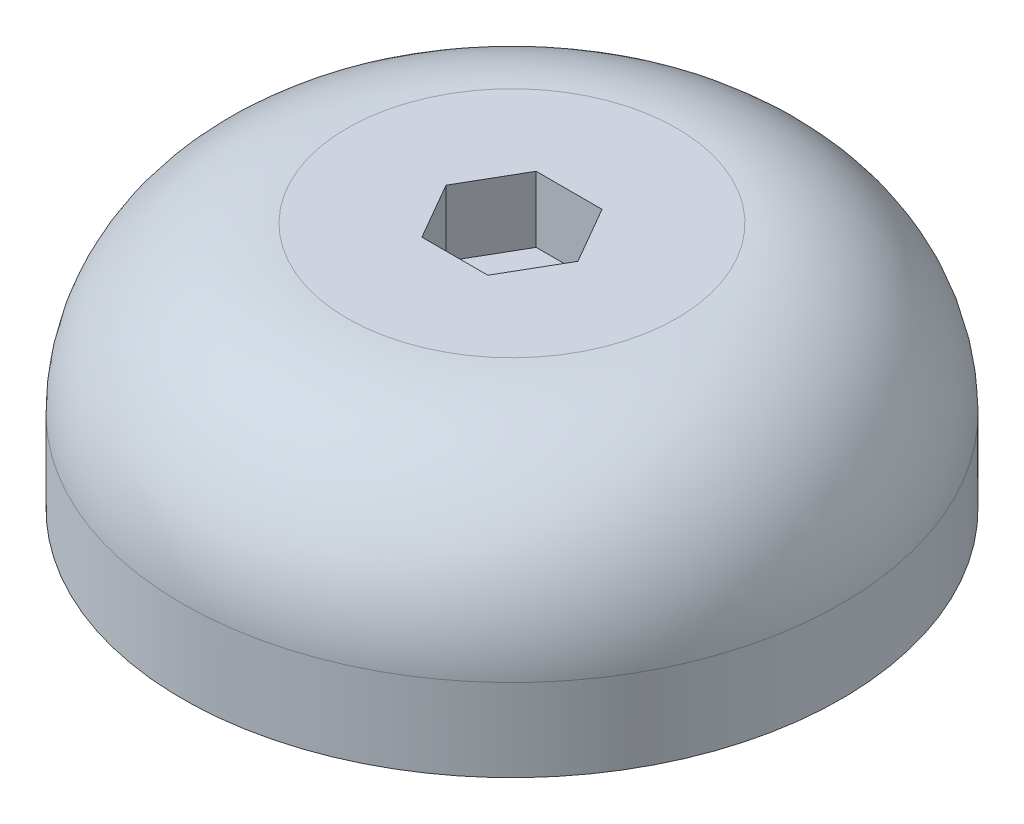
SolidWorks part; units mm, degrees
ref_plane "Front Plane" through (0, 0, 0) normal (0, 0, 1) x (1, 0, 0)
ref_plane "Top Plane" through (0, 0, 0) normal (0, 1, 0) x (1, 0, 0)
ref_plane "Right Plane" through (0, 0, 0) normal (1, 0, 0) x (0, 0, -1)
sketch "Sketch1" plane through (0, 0, 0) normal (0, 1, 0) x (1, 0, 0)
  circle A0 centre (0, 0) radius 9.75
  circle A1 centre (0, 0) radius 2
  dimension "D1" = 19.5
  dimension "D2" = 4
extrude "Boss-Extrude1" add sketch "Sketch1" along normal blind 3
sketch "Sketch2" plane through (0, 0, 0) normal (0, -1, 0) x (1, 0, 0)
  line L1 (-1.6303, -4.4164) -> (1.5697, -4.4164)
  line L2 (-1.6303, -4.4164) -> (-1.6303, -7.6164)
  line L3 (-1.6303, -7.6164) -> (1.5697, -7.6164)
  line L4 (1.5697, -4.4164) -> (1.5697, -7.6164)
  line L5 (-1.5303, -4.4664) -> (1.5032, -4.4664) construction
  line L6 (-1.5303, -4.4664) -> (-1.5303, -7.5) construction
  line L7 (-1.5303, -7.5) -> (1.5032, -7.5) construction
  line L8 (1.5032, -4.4664) -> (1.5032, -7.5) construction
  point P4 (-1.6355, -7.6164)
  dimension "D1" = 3.2
  dimension "D2" = 3.2
  dimension "D3" = 0.1
  dimension "D4" = 0.1
extrude "Cut-Extrude1" cut sketch "Sketch2" against normal blind 3
sketch "Sketch3" plane through (0, 3, 0) normal (0, 1, 0) x (1, 0, 0)
  circle A0 centre (0, 0) radius 20
  dimension "D1" = 40
extrude "Boss-Extrude2" add sketch "Sketch3" along normal blind 8
sketch "Sketch4" plane through (0, 3, 0) normal (0, -1, 0) x (1, 0, 0)
  circle A0 centre (0, 0) radius 9.75
  circle A1 centre (0, 0) radius 20
  circle A4 centre (0, 0) radius 20
  dimension "D1" = 0
extrude "Boss-Extrude3" add sketch "Sketch4" along normal blind 7
fillet "Fillet2" radius 10 1 edges at (0, 11, 20)
sketch "Sketch5" plane through (0, 3, 0) normal (0, -1, 0) x (1, 0, 0)
  circle A0 centre (0, 0) radius 2
  dimension "D1" = 4
extrude "Cut-Extrude2" cut sketch "Sketch5" against normal through all
sketch "Sketch6" plane through (0, 11, 0) normal (0, 1, 0) x (1, 0, 0)
  line L1 (4.001, 0) -> (2.0005, 3.465)
  line L2 (2.0005, 3.465) -> (-2.0005, 3.465)
  line L3 (-2.0005, 3.465) -> (-4.001, 0)
  line L4 (-4.001, 0) -> (-2.0005, -3.465)
  line L5 (-2.0005, -3.465) -> (2.0005, -3.465)
  line L6 (2.0005, -3.465) -> (4.001, 0)
  circle A0 centre (0, 0) radius 3.465 construction
  dimension "D1" = 6.93
extrude "Cut-Extrude3" cut sketch "Sketch6" against normal blind 4
fillet "Fillet3" radius 0.5 1 edges at (0, -4, -9.75)
